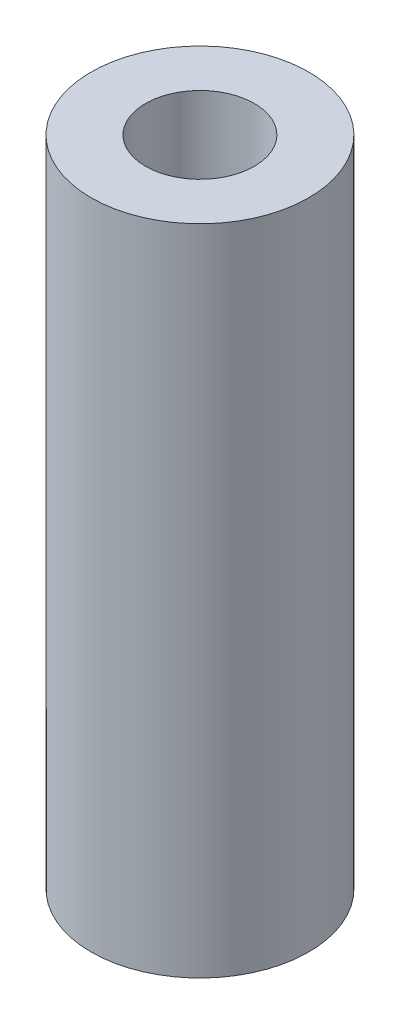
SolidWorks part; units mm, degrees
material "Nickel"
ref_plane "Plan de face" through (0, 0, 0) normal (0, 0, 1) x (1, 0, 0)
ref_plane "Plan de dessus" through (0, 0, 0) normal (0, 1, 0) x (1, 0, 0)
ref_plane "Plan de droite" through (0, 0, 0) normal (1, 0, 0) x (0, 0, -1)
sketch "Esquisse1" plane through (0, 0, 0) normal (0, 1, 0) x (1, 0, 0)
  circle A0 centre (0, 0) radius 3
  circle A1 centre (0, 0) radius 1.5
  dimension "D1" = 3
  dimension "D2" = 6
extrude "Boss.-Extru.1" add sketch "Esquisse1" along normal blind 18
